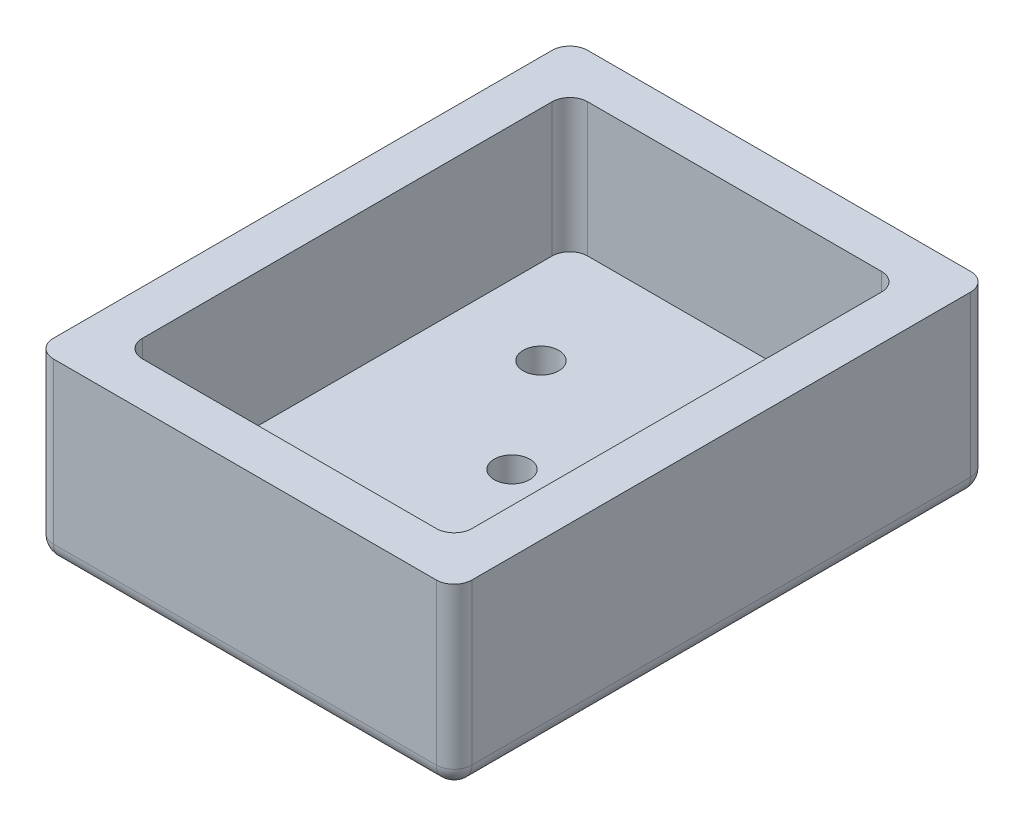
SolidWorks part; units mm, degrees
ref_plane "Front Plane" through (0, 0, 0) normal (0, 0, 1) x (1, 0, 0)
ref_plane "Top Plane" through (0, 0, 0) normal (0, 1, 0) x (1, 0, 0)
ref_plane "Right Plane" through (0, 0, 0) normal (1, 0, 0) x (0, 0, -1)
sketch "Sketch1" plane through (0, 0, 0) normal (0, 1, 0) x (1, 0, 0)
  line L9 (-20.8235, 25.4278) -> (26.1765, 25.4278)
  line L10 (-20.8235, 25.4278) -> (-20.8235, -34.5722)
  line L11 (-20.8235, -34.5722) -> (26.1765, -34.5722)
  line L12 (26.1765, 25.4278) -> (26.1765, -34.5722)
  point P4 (7.6765, 0.4278)
extrude "Boss-Extrude1" add sketch "Sketch1" along normal blind 20
shell "Shell1" thickness 5
fillet "Fillet2" radius 2 1 edges at (21.1765, 12.5, 29.5722)
fillet "Fillet3" radius 2 1 edges at (-15.8235, 12.5, 29.5722)
fillet "Fillet4" radius 2 1 edges at (-15.8235, 12.5, -20.4278)
fillet "Fillet5" radius 2 1 edges at (21.1765, 12.5, -20.4278)
fillet "Fillet6" radius 2 1 edges at (-20.8235, 10, 34.5722)
fillet "Fillet7" radius 2 1 edges at (26.1765, 10, 34.5722)
fillet "Fillet8" radius 2 1 edges at (-20.8235, 10, -25.4278)
fillet "Fillet9" radius 2 1 edges at (26.1765, 10, -25.4278)
fillet "Fillet10" radius 2 8 edges at (2.6765, 0, 34.5722) (-20.2377, 0, 33.9864) (26.1765, 0, 4.5722) (25.5907, 0, 33.9864) (-20.8235, 0, 4.5722) (-20.2377, 0, -24.842) (2.6765, 0, -25.4278) (25.5907, 0, -24.842)
sketch "Sketch2" plane through (0, 0, 0) normal (0, 1, 0) x (1, 0, 0)
  circle A2 centre (-6.2806, 7.6349) radius 2
  circle A3 centre (2.6765, -4.5722) radius 2
  circle A4 centre (11.6336, -16.7793) radius 2
extrude "Cut-Extrude1" cut sketch "Sketch2" along normal blind 10
